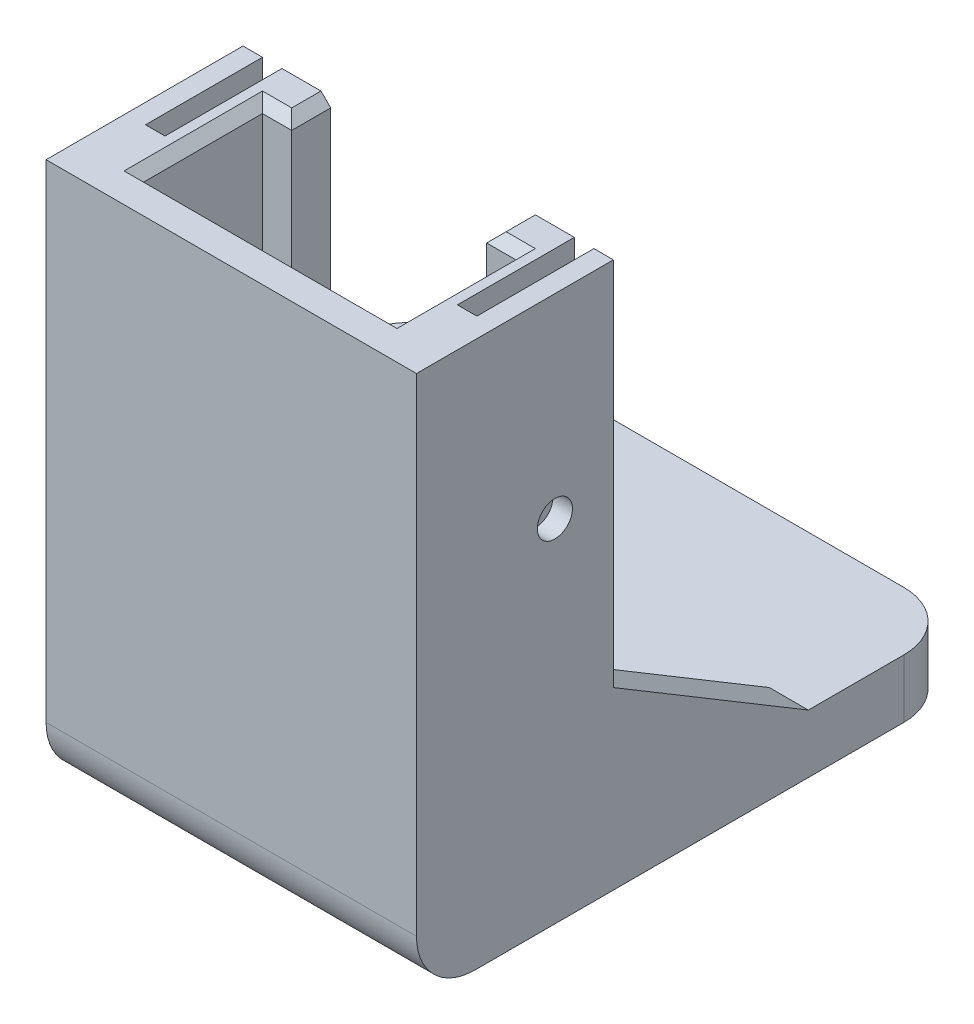
SolidWorks part; units mm, degrees
ref_plane "前视基准面" through (0, 0, 0) normal (0, 0, 1) x (1, 0, 0)
ref_plane "上视基准面" through (0, 0, 0) normal (0, 1, 0) x (1, 0, 0)
ref_plane "右视基准面" through (0, 0, 0) normal (1, 0, 0) x (0, 0, -1)
sketch "草图1" plane through (0, 0, 0) normal (0, 1, 0) x (1, 0, 0)
  line L0 (-57.4345, 0) -> (51.691, 0) construction
  line L1 (0, 59.2926) -> (0, -60.9819) construction
  line L2 (-9.5, 10.1) -> (-9.5, 0)
  line L3 (-9.5, 0) -> (9.5, 0)
  line L4 (9.5, 0) -> (9.5, 10.1)
  line L5 (9.5, 10.1) -> (5, 10.1)
  line L6 (-6.5, 8.1) -> (-6.5, 2)
  line L7 (-6.5, 2) -> (6.5, 2)
  line L8 (6.5, 2) -> (6.5, 8.1)
  line L9 (6.5, 8.1) -> (5, 8.1)
  line L10 (5, 8.1) -> (5, 10.1)
  line L11 (-6.5, 8.1) -> (-5, 8.1)
  line L12 (-5, 8.1) -> (-5, 10.1)
  line L13 (-5, 10.1) -> (-9.5, 10.1)
  dimension "D1" = 19
  dimension "D2" = 13
  dimension "D3" = 1.5
  dimension "D4" = 2
  dimension "D5" = 6.1
  dimension "D6" = 2
extrude "凸台-拉伸1" add sketch "草图1" along normal blind 25
sketch "草图2" plane through (0, 0, 0) normal (0, -1, 0) x (1, 0, 0)
  line L0 (9.5, 0) -> (-9.5, 0)
  line L1 (-9.5, 0) -> (-9.5, -28)
  line L2 (-9.5, -28) -> (9.5, -28)
  line L3 (9.5, -28) -> (9.5, 0)
  line L4 (0, -22.4608) -> (0, 12.6937) construction
  circle A0 centre (4, -25) radius 1.5
  circle A1 centre (-4, -25) radius 1.5
  dimension "D3" = 3
  dimension "D1" = 28
  dimension "D2" = 8
  dimension "D4" = 3
extrude "凸台-拉伸2" add sketch "草图2" along normal blind 3
sketch "草图3" plane through (0, 25, 0) normal (0, 1, 0) x (1, 0, 0)
  line L0 (-8.5, 10.1) -> (-7.5, 10.1)
  line L1 (-5, 10.1) -> (-9.5, 10.1) construction
  line L2 (-7.5, 10.1) -> (-7.5, 4.1)
  line L3 (-7.5, 4.1) -> (-8.5, 4.1)
  line L4 (-8.5, 4.1) -> (-8.5, 10.1)
  line L5 (-9.5, 10.1) -> (-9.5, 0) construction
  line L7 (0, 11.5268) -> (0, -2.7437) construction
  line L8 (8.5, 4.1) -> (8.5, 10.1)
  line L9 (7.5, 4.1) -> (8.5, 4.1)
  line L10 (7.5, 10.1) -> (7.5, 4.1)
  line L11 (8.5, 10.1) -> (7.5, 10.1)
  dimension "D1" = 1
  dimension "D2" = 1
  dimension "D3" = 6
extrude "切除-拉伸1" cut sketch "草图3" against normal blind 15
sketch "草图4" plane through (-9.5, 0, 0) normal (-1, 0, 0) x (0, 0, 1)
  line L1 (-10.1, 25) -> (-10.1, 0) construction
  line L2 (-10.1, 25) -> (0, 25) construction
  circle A0 centre (-7.1, 15) radius 0.9
  dimension "D1" = 1.8
  dimension "D2" = 3
  dimension "D3" = 10
extrude "切除-拉伸2" cut sketch "草图4" against normal up to surface (19 mm away) up to face at (9.5, 7.3333, -12.7)
fillet "圆角1" radius 3 2 edges at (9.5, -1.5, -28) (-9.5, -1.5, -28)
sketch "草图5" plane through (-9.5, 0, 0) normal (-1, 0, 0) x (0, 0, 1)
  line L0 (-10.1, 0) -> (-10.1, 6)
  line L1 (-10.1, 25) -> (-10.1, 0) construction
  line L2 (-10.1, 6) -> (-20.1, 0)
  line L3 (-10.1, 0) -> (-25, 0) construction
  line L4 (-20.1, 0) -> (-10.1, 0)
  dimension "D1" = 10
  dimension "D2" = 6
extrude "凸台-拉伸3" add sketch "草图5" against normal blind 2
mirror "镜向1" about plane through (0, 0, 0) normal (1, 0, 0) of "凸台-拉伸3"
sketch "草图6" plane through (0, 0, 0) normal (0, 1, 0) x (1, 0, 0)
  line L0 (-6.5, 2) -> (6.5, 2)
  line L1 (6.5, 2) -> (6.5, 8.1)
  line L2 (6.5, 8.1) -> (5, 8.1)
  line L3 (-6.5, 8.1) -> (-6.5, 2)
  line L4 (-5, 8.1) -> (-5, 10.1)
  line L5 (-5, 10.1) -> (5, 10.1)
  line L6 (5, 10.1) -> (5, 8.1)
  line L7 (-5, 8.1) -> (-6.5, 8.1)
extrude "凸台-拉伸4" add sketch "草图6" along normal blind 5
fillet "圆角2" radius 3 1 edges at (0, -3, 0)
chamfer "倒角1" distance 0.5 angle 45 7 edges at (5, 25, -9.1) (-5, 25, -9.1) (-5.75, 25, -8.1) (5.75, 25, -8.1) (6.5, 25, -5.05) (0, 25, -2) (-6.5, 25, -5.05)
sketch "草图7" plane through (0, 0, 0) normal (0, 1, 0) x (1, 0, 0)
  line L0 (6.5, 28) -> (-15.798, 28)
  line L1 (-18.798, 25) -> (-18.798, 23.1)
  line L2 (-15.798, 20.1) -> (6.5, 20.1)
  line L3 (6.5, 20.1) -> (6.5, 28)
  line L4 (-7.5, 20.1) -> (-9.5, 20.1) construction
  circle A1 centre (-13.798, 23) radius 1.5 construction
  circle A2 centre (-5.798, 23) radius 1.5 construction
  arc A5 (-15.798, 20.1) -> (-18.798, 23.1) centre (-15.798, 23.1) cw
  arc A6 (-18.798, 25) -> (-15.798, 28) centre (-15.798, 25) cw
  dimension "D1" = 3
  dimension "D6" = 3
  dimension "D2" = 8
  dimension "D3" = 5
  dimension "D5" = 5
extrude "凸台-拉伸5" add sketch "草图7" against normal up to surface (3 mm away) up to face at (4, -3, -26.5)
hole_wizard "Ø3.0 (3) 直径孔1" positions "草图8" profile "草图9" hole size "Ø3.0" standard "GB" end condition up to next
sketch "草图8" plane through (0, 0, 0) normal (0, 1, 0) x (1, 0, 0)
  point P0 (-5.798, 23)
  point P3 (-13.798, 23)
sketch "草图9" plane through (-5.798, 0, -23) normal (1, 0, 0) x (0, 0, 1)
  line L0 (0, 0) -> (0, 3)
  line L1 (0, 3) -> (1.5, 3)
  line L2 (1.5, 3) -> (1.5, 0)
  line L5 (1.5, 0) -> (0, 0)
  line L11 (0, -6.35) -> (0, 107.95) construction
  dimension "通孔孔直径" = 3
  dimension "通孔孔深度" = 3
